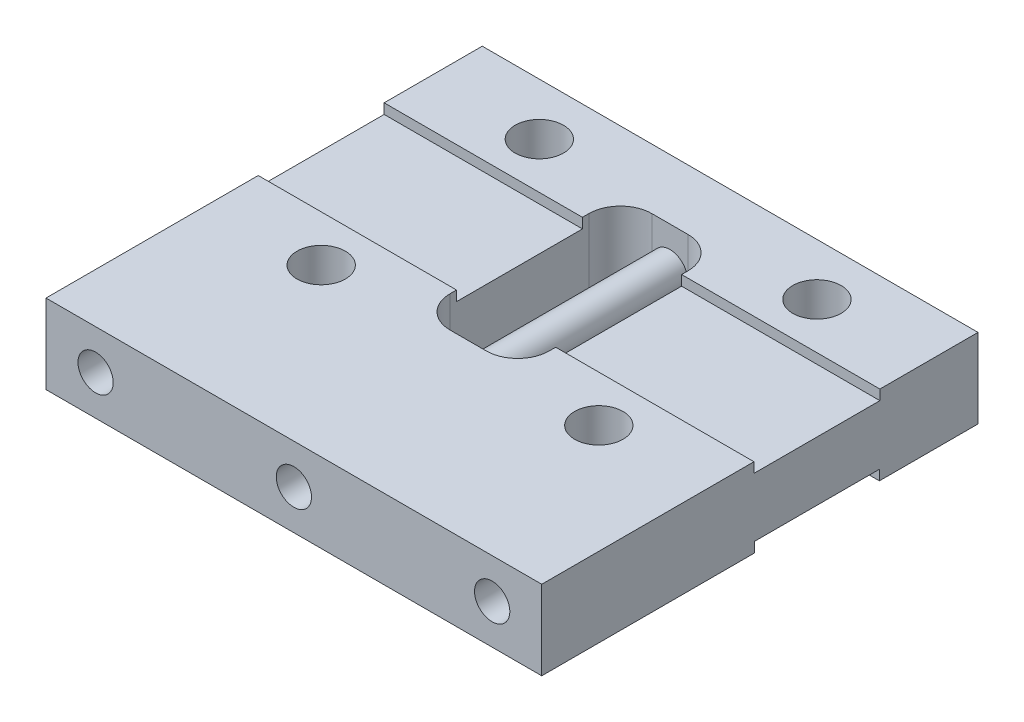
SolidWorks part; units mm, degrees
ref_plane "Plano frontal" through (0, 0, 0) normal (0, 0, 1) x (1, 0, 0)
ref_plane "Plano superior" through (0, 0, 0) normal (0, 1, 0) x (1, 0, 0)
ref_plane "Plano direito" through (0, 0, 0) normal (1, 0, 0) x (0, 0, -1)
ref_plane "Plano1" through (0, 0, 0) normal (0, -1, 0) x (1, 0, 0)
sketch "Esboço1" plane through (0, 0, 0) normal (0, -1, 0) x (1, 0, 0)
  line L0 (0, 0) -> (25, 0)
  line L1 (25, 0) -> (25, 22)
  line L2 (25, 22) -> (0, 22)
  line L3 (0, 22) -> (0, 0)
extrude "Ressalto-extrusão1" add sketch "Esboço1" against normal blind 4
sketch "Esboço2" plane through (0, 0, 0) normal (0, -1, 0) x (1, 0, 0)
  line L0 (10, 13.21) -> (10, 3.035)
  line L1 (10, 3.035) -> (15, 3.035)
  line L2 (15, 3.035) -> (15, 13.21)
  line L3 (15, 13.21) -> (10, 13.21)
extrude "Corte-extrusão1" cut sketch "Esboço2" against normal through all
sketch "Esboço3" plane through (25, 0, 0) normal (1, 0, 0) x (0, 0, -1)
  line L0 (-11.2725, 0) -> (-4.9725, 0)
  line L1 (-4.9725, 0) -> (-4.9725, 0.508)
  line L2 (-4.9725, 0.508) -> (-11.2725, 0.508)
  line L3 (-11.2725, 0.508) -> (-11.2725, 0)
extrude "Corte-extrusão2" cut sketch "Esboço3" against normal up to next
sketch "Esboço4" plane through (10, 0, 0) normal (1, 0, 0) x (0, 0, -1)
  line L0 (-11.2725, 0) -> (-4.9725, 0)
  line L1 (-4.9725, 0) -> (-4.9725, 0.508)
  line L2 (-4.9725, 0.508) -> (-11.2725, 0.508)
  line L3 (-11.2725, 0.508) -> (-11.2725, 0)
extrude "Corte-extrusão3" cut sketch "Esboço4" against normal through all
sketch "Esboço5" plane through (10, 0, 0) normal (1, 0, 0) x (0, 0, -1)
  line L0 (-4.9475, 4) -> (-11.2975, 4)
  line L1 (-11.2975, 4) -> (-11.2975, 3.492)
  line L2 (-11.2975, 3.492) -> (-4.9475, 3.492)
  line L3 (-4.9475, 3.492) -> (-4.9475, 4)
extrude "Corte-extrusão4" cut sketch "Esboço5" against normal through all
sketch "Esboço6" plane through (25, 0, 0) normal (1, 0, 0) x (0, 0, -1)
  line L0 (-11.2975, 4) -> (-11.2975, 3.492)
  line L1 (-11.2975, 3.492) -> (-4.9475, 3.492)
  line L2 (-4.9475, 3.492) -> (-4.9475, 4)
  line L3 (-4.9475, 4) -> (-11.2975, 4)
extrude "Corte-extrusão5" cut sketch "Esboço6" against normal through all
hole_wizard "Furo com folga de M21" positions "Esboço8" profile "Esboço7" hole size "M2" standard "Ansi Metric"
sketch "Esboço8" plane through (0, 0, 0) normal (0, -1, 0) x (-1, 0, 0)
  point P0 (-19.5, -13.6225)
  point P1 (-19.5, -2.6225)
  point P2 (-5.5, -2.6225)
  point P3 (-5.5, -13.6225)
sketch "Esboço7" plane through (19.5, 0, 13.6225) normal (1, 0, 0) x (0, 0, -1)
  line L0 (0, 0) -> (0, 4)
  line L1 (0, 4) -> (1.2192, 4)
  line L2 (1.2192, 4) -> (1.2192, 0)
  line L5 (1.2192, 0) -> (0, 0)
  line L11 (0, -6.35) -> (0, 107.95) construction
  dimension "Thru Hole Dia." = 2.4384
  dimension "Thru Hole Depth" = 4
hole_wizard "Furo com folga de M1.61" positions "Esboço10" profile "Esboço9" hole size "M1.6" standard "Ansi Metric"
sketch "Esboço10" plane through (0, 0, 0) normal (0, 0, -1) x (-1, 0, 0)
  point P0 (-2.5, 2)
  point P1 (-22.5, 2)
sketch "Esboço9" plane through (2.5, 2, 0) normal (1, 0, 0) x (0, 1, 0)
  line L0 (0, 0) -> (0, 22)
  line L1 (0, 22) -> (0.889, 22)
  line L2 (0.889, 22) -> (0.889, 0)
  line L5 (0.889, 0) -> (0, 0)
  line L11 (0, -6.35) -> (0, 107.95) construction
  dimension "Thru Hole Dia." = 1.778
  dimension "Thru Hole Depth" = 22
hole_wizard "Furo com folga de M1.62" positions "Esboço12" profile "Esboço11" hole size "M1.6" standard "Ansi Metric"
sketch "Esboço12" plane through (0, 0, 0) normal (0, 0, -1) x (-1, 0, 0)
  point P0 (-12.5, 2)
sketch "Esboço11" plane through (12.5, 2, 0) normal (1, 0, 0) x (0, 1, 0)
  line L0 (0, 0) -> (0, 3.035)
  line L1 (0, 3.035) -> (0.889, 3.035)
  line L2 (0.889, 3.035) -> (0.889, 0)
  line L5 (0.889, 0) -> (0, 0)
  line L11 (0, -6.35) -> (0, 107.95) construction
  dimension "Thru Hole Dia." = 1.778
  dimension "Thru Hole Depth" = 3.035
hole_wizard "Furo com folga de M1.63" positions "Esboço14" profile "Esboço13" hole size "M1.6" standard "Ansi Metric"
sketch "Esboço14" plane through (0, 0, 22) normal (0, 0, 1) x (1, 0, 0)
  point P0 (12.5, 2)
sketch "Esboço13" plane through (12.5, 2, 22) normal (1, 0, 0) x (0, -1, 0)
  line L0 (0, 0) -> (0, 22)
  line L1 (0, 22) -> (0.889, 22)
  line L2 (0.889, 22) -> (0.889, 0)
  line L5 (0.889, 0) -> (0, 0)
  line L11 (0, -6.35) -> (0, 107.95) construction
  dimension "Thru Hole Dia." = 1.778
  dimension "Thru Hole Depth" = 22
fillet "Filete1" radius 1.5875 4 edges at (15, 2, 13.21) (10, 2, 13.21) (15, 2, 3.035) (10, 2, 3.035)
sketch "Esboço15" plane through (0, 0, 0) normal (0, 0, -1) x (-1, 0, 0)
  circle A0 centre (-2.5, 2) radius 0.889
  circle A1 centre (-12.5, 2) radius 0.889
  circle A2 centre (-22.5, 2) radius 0.889
extrude "Ressalto-extrusão2" add sketch "Esboço15" against normal blind 16
